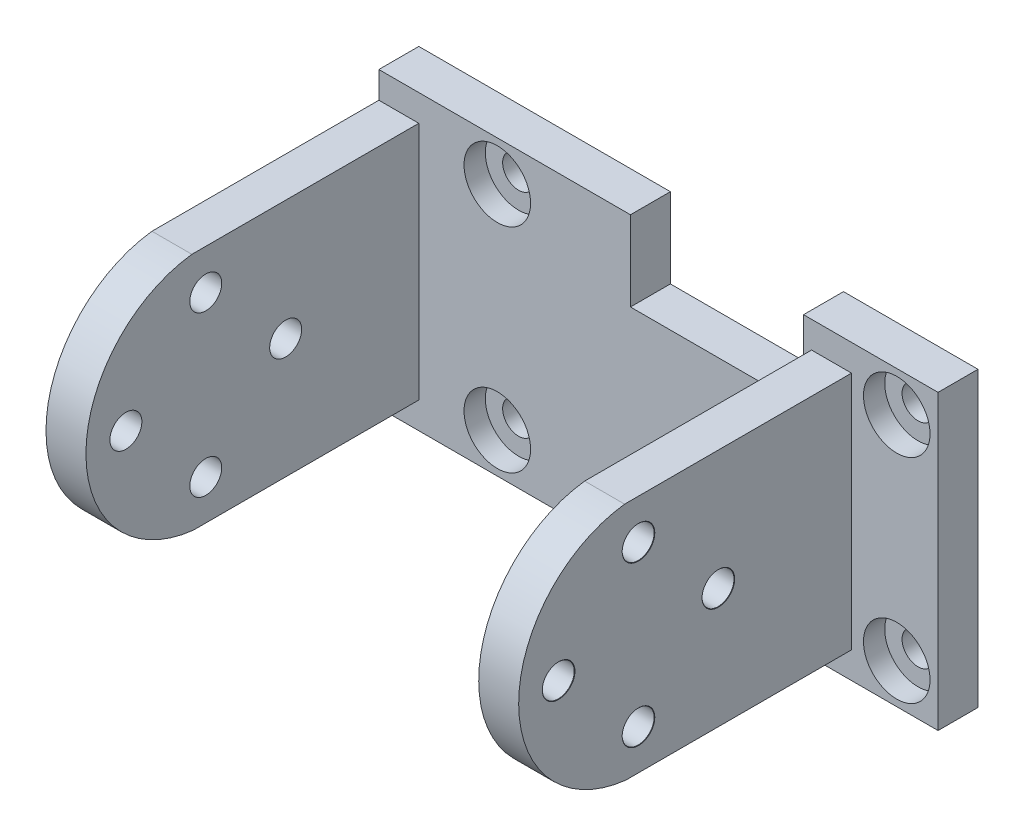
SolidWorks part; units mm, degrees
ref_plane "Front Plane" through (0, 0, 0) normal (0, 0, 1) x (1, 0, 0)
ref_plane "Top Plane" through (0, 0, 0) normal (0, 1, 0) x (1, 0, 0)
ref_plane "Right Plane" through (0, 0, 0) normal (1, 0, 0) x (0, 0, -1)
ref_plane "Plane1" through (0, 0, 163.527) normal (0, 0, 1) x (1, 0, 0)
sketch "Sketch1" plane through (0, 0, 163.527) normal (0, 0, 1) x (1, 0, 0)
  line L0 (36.2066, 229.3346) -> (-5.7934, 229.3346)
  line L1 (-5.7934, 229.3346) -> (-5.7934, 207.3346)
  line L2 (-5.7934, 207.3346) -> (36.2066, 207.3346)
  line L3 (36.2066, 207.3346) -> (36.2066, 229.3346)
extrude "Boss-Extrude1" add sketch "Sketch1" against normal blind 3
sketch "Sketch2" plane through (0, 0, 160.527) normal (0, 0, -1) x (-1, 0, 0)
  line L0 (-13.1033, 229.3346) -> (-26.1033, 229.3346)
  line L1 (-26.1033, 229.3346) -> (-26.1033, 223.3346)
  line L2 (-26.1033, 223.3346) -> (-13.1033, 223.3346)
  line L3 (-13.1033, 223.3346) -> (-13.1033, 229.3346)
extrude "Cut-Extrude1" cut sketch "Sketch2" against normal through all
sketch "Sketch3" plane through (0, 0, 160.527) normal (0, 0, -1) x (-1, 0, 0)
  line L0 (-26.1033, 207.3346) -> (-13.1033, 207.3346)
  line L1 (-13.1033, 207.3346) -> (-13.1033, 213.3346)
  line L2 (-13.1033, 213.3346) -> (-26.1033, 213.3346)
  line L3 (-26.1033, 213.3346) -> (-26.1033, 207.3346)
extrude "Cut-Extrude2" cut sketch "Sketch3" against normal through all
ref_plane "Plane2" through (-5.7934, 0, 0) normal (-1, 0, 0) x (0, -1, 0)
sketch "Sketch4" plane through (-5.7934, 0, 0) normal (-1, 0, 0) x (0, -1, 0)
  line L0 (-227.3346, 180.5701) -> (-227.3346, 163.527)
  line L1 (-227.3346, 163.527) -> (-209.3346, 163.527)
  line L2 (-209.3346, 163.527) -> (-209.3346, 180.4739)
  arc A0 (-209.3346, 180.4739) -> (-227.3346, 180.5701) centre (-218.3403, 179.465) ccw
extrude "Boss-Extrude2" add sketch "Sketch4" against normal blind 3
ref_plane "Plane3" through (29.7066, 0, 0) normal (1, 0, 0) x (0, 0, -1)
sketch "Sketch5" plane through (29.7066, 0, 0) normal (1, 0, 0) x (0, 0, -1)
  line L0 (-180.4739, 209.3346) -> (-163.527, 209.3346)
  line L1 (-163.527, 209.3346) -> (-163.527, 227.3346)
  line L2 (-163.527, 227.3346) -> (-180.5701, 227.3346)
  arc A0 (-180.5701, 227.3346) -> (-180.4739, 209.3346) centre (-179.465, 218.3403) ccw
extrude "Boss-Extrude3" add sketch "Sketch5" against normal blind 3
hole_wizard "M2 Clearance Hole1" positions "Sketch7" profile "Sketch6" hole size "M2" standard "ANSI Metric" end condition through all
sketch "Sketch7" plane through (29.7066, 0, 0) normal (1, 0, 0) x (0, 0, -1)
  point P0 (-179.5272, 224.3342)
  point P1 (-185.527, 218.3344)
  point P2 (-179.5272, 212.3346)
  point P3 (-173.5274, 218.3344)
sketch "Sketch6" plane through (29.7066, 224.3342, 179.5272) normal (0, 1, 0) x (0, 0, -1)
  line L0 (0, 0) -> (0, 35.5)
  line L1 (0, 35.5) -> (1.2, 35.5)
  line L2 (1.2, 35.5) -> (1.2, 0.025)
  line L3 (1.2, 0.025) -> (1.225, 0)
  line L5 (1.225, 0) -> (0, 0)
  line L6 (-1.2, 0.025) -> (-1.225, 0) construction
  line L11 (0, -6.35) -> (0, 107.95) construction
  dimension "Thru Hole Dia." = 2.4
  dimension "Thru Hole Depth" = 35.5
  dimension "Near C'Sink Dia." = 2.45
  dimension "Near C'Sink Angle" = 90
hole_wizard "M2 Clearance Hole2" positions "Sketch9" profile "Sketch8" hole size "M2" standard "ANSI Metric" end condition through all
sketch "Sketch9" plane through (0, 0, 163.527) normal (0, 0, 1) x (1, 0, 0)
  point P0 (3.1033, 226.327)
  point P1 (3.1033, 210.327)
  point P2 (33.1033, 210.327)
  point P3 (33.1033, 226.327)
sketch "Sketch8" plane through (3.1033, 226.327, 163.527) normal (1, 0, 0) x (0, -1, 0)
  line L0 (0, 0) -> (0, 3)
  line L1 (0, 3) -> (1.2, 3)
  line L2 (1.2, 3) -> (1.2, 0)
  line L5 (1.2, 0) -> (0, 0)
  line L11 (0, -6.35) -> (0, 107.95) construction
  dimension "Thru Hole Dia." = 2.4
  dimension "Thru Hole Depth" = 3
hole_wizard "Ø2.0 (2) Diameter Hole2" positions "Sketch11" profile "Sketch10" hole size "Ø2.0" standard "ANSI Metric"
sketch "Sketch11" plane through (-5.7934, 0, 0) normal (-1, 0, 0) x (0, 0, 1)
  point P0 (179.5272, 224.3342)
  point P1 (185.527, 218.3344)
  point P2 (179.5272, 212.3346)
  point P3 (173.5274, 218.3344)
sketch "Sketch10" plane through (-5.7934, 224.3342, 179.5272) normal (0, 1, 0) x (0, 0, 1)
  line L0 (0, 0) -> (0, 42)
  line L1 (0, 42) -> (1, 42)
  line L2 (1, 42) -> (1, 1.8)
  line L3 (1, 1.8) -> (2.8, 0)
  line L5 (2.8, 0) -> (0, 0)
  line L6 (-1, 1.8) -> (-2.8, 0) construction
  line L11 (0, -6.35) -> (0, 107.95) construction
  dimension "Thru Hole Dia." = 2
  dimension "Thru Hole Depth" = 42
  dimension "Near C'Sink Dia." = 5.6
  dimension "Near C'Sink Angle" = 90
sketch "Sketch12" plane through (0, 0, 163.527) normal (0, 0, 1) x (1, 0, 0)
  point P0 (3.1033, 226.327)
  point P3 (3.1033, 210.327)
  point P6 (33.1033, 226.327)
  point P9 (33.1033, 210.327)
hole_wizard "CBORE for M2 Pan Head Machine Screw2" positions "Sketch12" profile "Sketch13" counterbore size "M2" standard "ANSI Metric" end condition through all
sketch "Sketch13" plane through (3.1033, 226.327, 163.527) normal (1, 0, 0) x (0, -1, 0)
  line L0 (0, 0) -> (0, 3)
  line L1 (0, 3) -> (1.2, 3)
  line L3 (1.2, 3) -> (1.2, 1.6)
  line L4 (1.2, 1.6) -> (2.5, 1.6)
  line L5 (2.5, 1.6) -> (2.5, 0)
  line L7 (2.5, 0) -> (0, 0)
  line L11 (0, -6.35) -> (0, 107.95) construction
  dimension "Thru Hole Dia." = 2.4
  dimension "Thru Hole Depth" = 3
  dimension "C'Bore Dia." = 5
  dimension "C'Bore Depth" = 1.6
